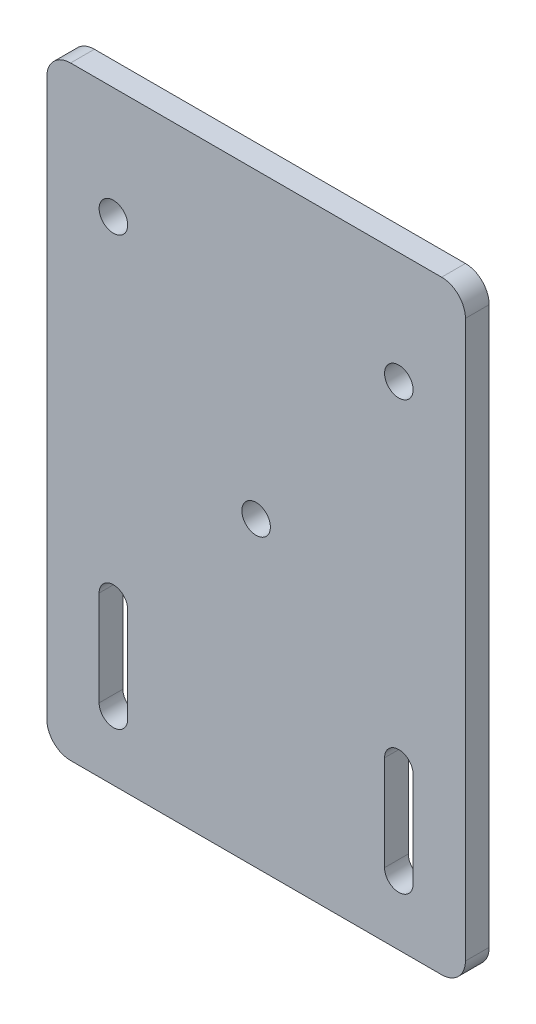
SolidWorks part; units mm, degrees
ref_plane "Front Plane" through (0, 0, 0) normal (0, 0, 1) x (1, 0, 0)
ref_plane "Top Plane" through (0, 0, 0) normal (0, 1, 0) x (1, 0, 0)
ref_plane "Right Plane" through (0, 0, 0) normal (1, 0, 0) x (0, 0, -1)
sketch "Sketch1" plane through (0, 0, 0) normal (0, 0, 1) x (1, 0, 0)
  line L1 (-39, -63.5) -> (39, -63.5)
  line L2 (-44, -58.5) -> (-44, 58.5)
  line L3 (-39, 63.5) -> (39, 63.5)
  line L4 (44, -58.5) -> (44, 58.5)
  line L5 (27, -30) -> (27, -50)
  line L6 (33, -30) -> (33, -50)
  line L7 (-33, -30) -> (-33, -50)
  line L8 (-27, -30) -> (-27, -50)
  circle A0 centre (-30, 40) radius 3
  circle A1 centre (30, 40) radius 3
  arc A4 (-27, -30) -> (-33, -30) centre (-30, -30) ccw
  arc A5 (-33, -50) -> (-27, -50) centre (-30, -50) ccw
  arc A6 (33, -50) -> (27, -50) centre (30, -50) cw
  arc A7 (27, -30) -> (33, -30) centre (30, -30) cw
  circle A8 centre (0, 0) radius 3
  arc A9 (44, 58.5) -> (39, 63.5) centre (39, 58.5) ccw
  arc A10 (44, -58.5) -> (39, -63.5) centre (39, -58.5) cw
  arc A11 (-39, -63.5) -> (-44, -58.5) centre (-39, -58.5) cw
  arc A12 (-44, 58.5) -> (-39, 63.5) centre (-39, 58.5) cw
  point P0 (0, 0)
  point P26 (44, 63.5)
  point P29 (44, -63.5)
  point P34 (-44, 63.5)
  dimension "D3" = 5
  dimension "D1" = 127
  dimension "D2" = 88
extrude "Boss-Extrude1" add sketch "Sketch1" along normal blind 5
